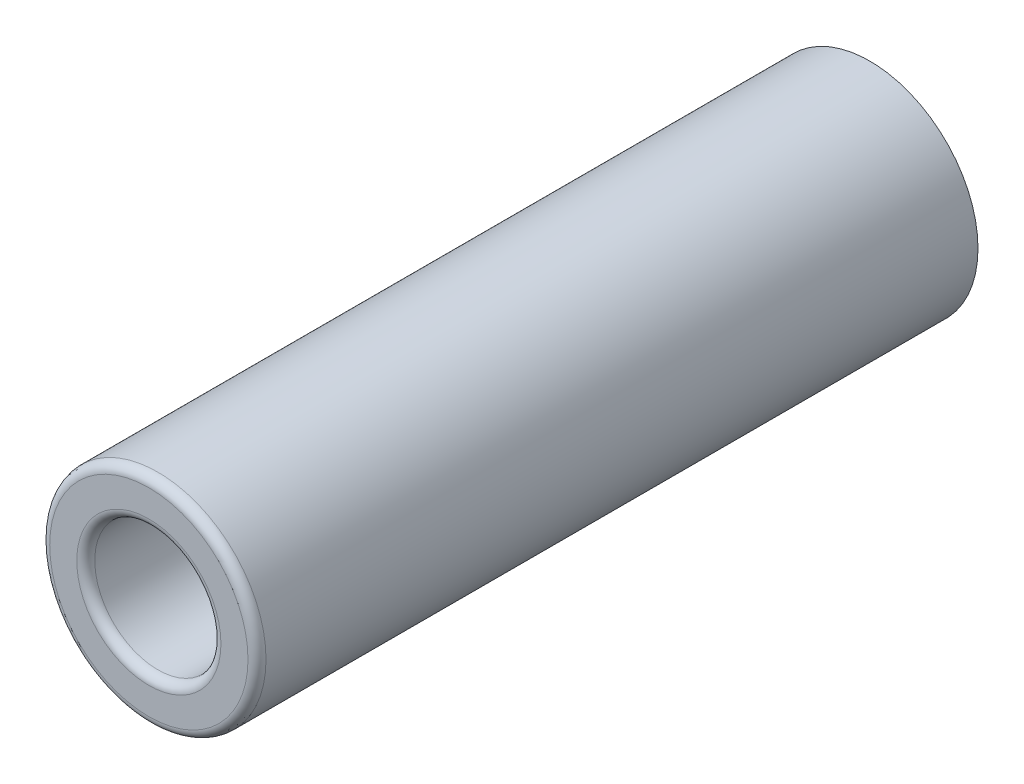
SolidWorks part; units mm, degrees
ref_plane "Płaszczyzna przednia" through (0, 0, 0) normal (0, 0, 1) x (1, 0, 0)
ref_plane "Płaszczyzna górna" through (0, 0, 0) normal (0, 1, 0) x (1, 0, 0)
ref_plane "Płaszczyzna prawa" through (0, 0, 0) normal (1, 0, 0) x (0, 0, -1)
sketch "Szkic1" plane through (0, 0, 0) normal (0, 0, 1) x (1, 0, 0)
  circle A0 centre (0, 0) radius 3.5
  circle A1 centre (0, 0) radius 6
  dimension "D1" = 7
  dimension "D2" = 12
extrude "Dodanie-wyciągnięcie1" add sketch "Szkic1" along normal blind 40
fillet "Zaokrąglenie1" radius 0.5 1 edges at (6, 0, 40)
fillet "Zaokrąglenie2" radius 0.5 1 edges at (3.5, 0, 40)
